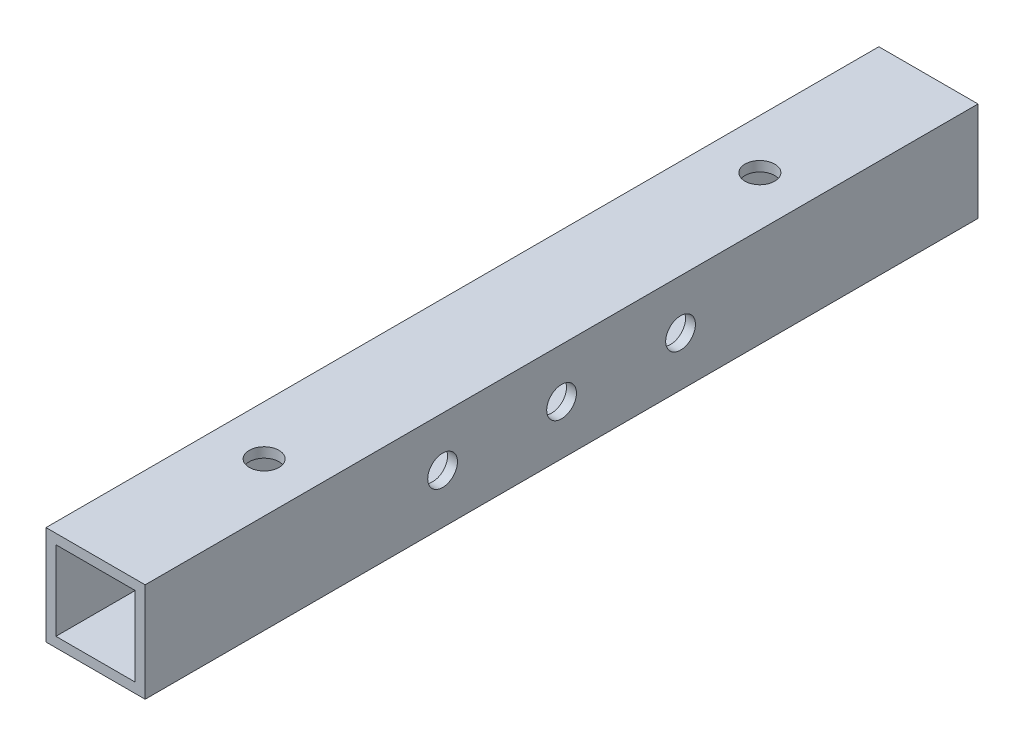
SolidWorks part; units mm, degrees
material "6063-O"
ref_plane "前视基准面" through (0, 0, 0) normal (0, 0, 1) x (1, 0, 0)
ref_plane "上视基准面" through (0, 0, 0) normal (0, 1, 0) x (1, 0, 0)
ref_plane "右视基准面" through (0, 0, 0) normal (1, 0, 0) x (0, 0, -1)
other "Configuration Table"
sketch "草图1" plane through (0, 0, 0) normal (0, 0, 1) x (1, 0, 0)
  line L1 (-5, 5) -> (5, 5)
  line L2 (-5, 5) -> (-5, -5)
  line L3 (-5, -5) -> (5, -5)
  line L4 (5, 5) -> (5, -5)
  line L5 (-5, 5) -> (5, -5) construction
  line L6 (-5, -5) -> (5, 5) construction
  point P4 (0, 0)
  dimension "D1" = 10
  dimension "D2" = 10
extrude "拉伸-薄壁1" add sketch "草图1" along normal blind 84 thin
sketch "草图2" plane through (5, 0, 0) normal (1, 0, 0) x (0, 0, -1)
  line L0 (-84, 0) -> (0, 0) construction
  line L1 (-84, -5) -> (-84, 5) construction
  line L2 (0, -5) -> (0, 5) construction
  line L3 (-42, 5) -> (-42, -5) construction
  line L4 (-84, 5) -> (0, 5) construction
  line L5 (-84, -5) -> (0, -5) construction
  circle A0 centre (-69, 0) radius 1.5 construction
  circle A1 centre (-54, 0) radius 1.5
  circle A2 centre (-30, 0) radius 1.5
  circle A3 centre (-15, 0) radius 1.5 construction
  circle A4 centre (-42, 0) radius 1.5 construction
  circle A5 centre (-42, 0) radius 1.5
  dimension "D1" = 3
  dimension "D2" = 15
  dimension "D3" = 12
extrude "切除-拉伸1" cut sketch "草图2" against normal through all
sketch "草图3" plane through (0, -5, 0) normal (0, -1, 0) x (1, 0, 0)
  line L0 (0, 84) -> (0, 0) construction
  line L1 (-5, 84) -> (5, 84) construction
  line L2 (-5, 0) -> (5, 0) construction
  line L3 (5, 42) -> (-5, 42) construction
  line L4 (5, 84) -> (5, 0) construction
  line L5 (-5, 84) -> (-5, 0) construction
  circle A0 centre (0, 54) radius 1.5 construction
  circle A1 centre (0, 30) radius 1.5 construction
  circle A2 centre (0, 42) radius 1.5 construction
  circle A3 centre (0, 17) radius 1.5
  circle A4 centre (0, 67) radius 1.5
  dimension "D1" = 3
  dimension "D2" = 24
  dimension "D3" = 25
  dimension "D4" = 15.5
extrude "切除-拉伸2" cut sketch "草图3" against normal through all
